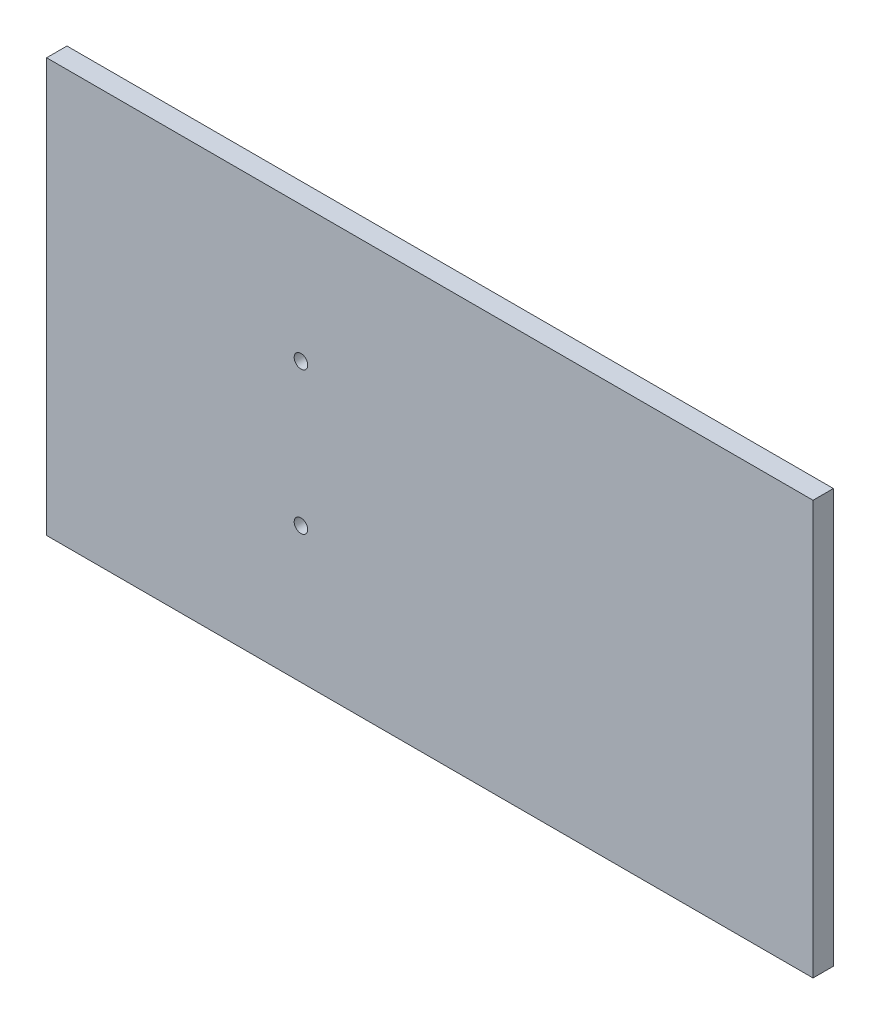
SolidWorks part; units mm, degrees
ref_plane "Front Plane" through (0, 0, 0) normal (0, 0, 1) x (1, 0, 0)
ref_plane "Top Plane" through (0, 0, 0) normal (0, 1, 0) x (1, 0, 0)
ref_plane "Right Plane" through (0, 0, 0) normal (1, 0, 0) x (0, 0, -1)
sketch "Sketch1" plane through (0, 0, 0) normal (0, 0, 1) x (1, 0, 0)
  line L9 (-113, 61) -> (0, 61)
  line L10 (-113, 61) -> (-113, 0)
  line L11 (-113, 0) -> (0, 0)
  line L12 (0, 61) -> (0, 0)
  circle A0 centre (-75.5, 41) radius 1
  circle A1 centre (-75.5, 20) radius 1
  dimension "D10" = 2
  dimension "D11" = 2
  dimension "D2" = 113
  dimension "D3" = 61
  dimension "D12" = 75.5
  dimension "D13" = 20
  dimension "D14" = 20
extrude "Boss-Extrude1" add sketch "Sketch1" along normal blind 3
